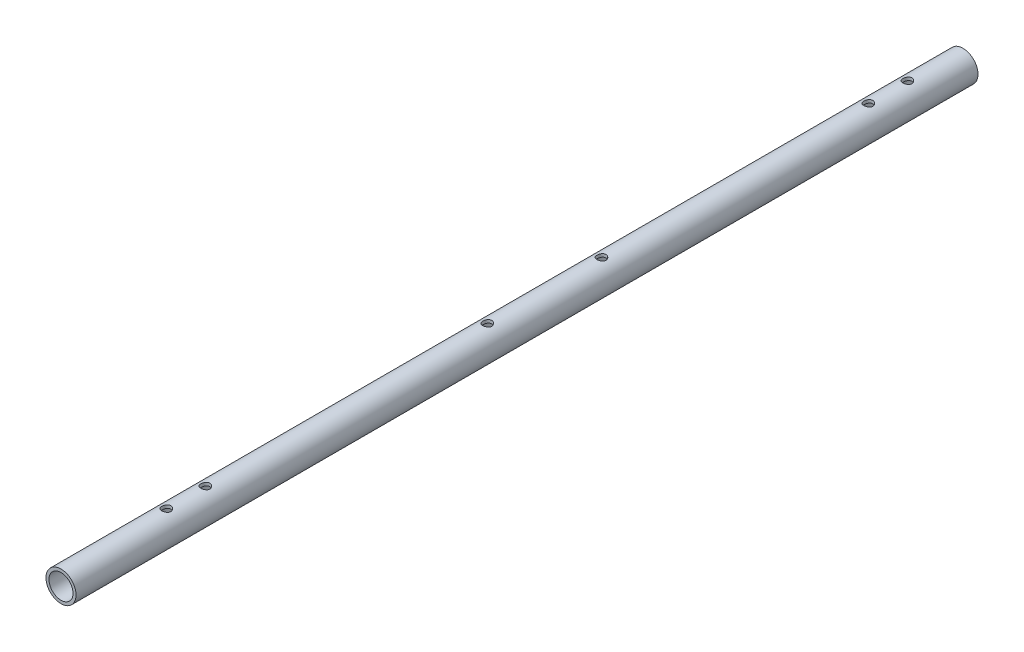
SolidWorks part; units mm, degrees
ref_plane "前视基准面" through (0, 0, 0) normal (0, 0, 1) x (1, 0, 0)
ref_plane "上视基准面" through (0, 0, 0) normal (0, 1, 0) x (1, 0, 0)
ref_plane "右视基准面" through (0, 0, 0) normal (1, 0, 0) x (0, 0, -1)
sketch "草图1" plane through (0, 0, 0) normal (0, 0, 1) x (1, 0, 0)
  circle A0 centre (0, 0) radius 5
  dimension "D1" = 10
extrude "拉伸-薄壁1" add sketch "草图1" along normal mid plane 300 thin thin type one direction reverse wall 1
sketch "草图2" plane through (0, 0, 0) normal (0, 1, 0) x (1, 0, 0)
  line L0 (0, 29.75) -> (0, -8.25) construction
  line L1 (-5, -150) -> (5, -150) construction
  circle A0 centre (0, 29.75) radius 1.5
  circle A1 centre (0, -8.25) radius 1.5
  circle A2 centre (0, 10.75) radius 1.5 construction
  dimension "D1" = 3
  dimension "D2" = 141.75
  dimension "D3" = 38
extrude "切除-拉伸1" cut sketch "草图2" against normal through all both and the other way through all
sketch "草图3" plane through (0, 0, 0) normal (0, 1, 0) x (0, 0, -1)
  line L0 (150, -5) -> (150, 5) construction
  line L1 (131.5, 0) -> (150, 0) construction
  line L2 (-115, 0) -> (-102, 0) construction
  line L3 (-150, 5) -> (-150, -5) construction
  circle A0 centre (118.5, 0) radius 1.5
  circle A1 centre (131.5, 0) radius 1.5
  circle A2 centre (-115, 0) radius 1.5
  circle A3 centre (-102, 0) radius 1.5
  point P11 (-108.5, 0)
  dimension "D1" = 13
  dimension "D2" = 3
  dimension "D3" = 18.5
  dimension "D4" = 13
  dimension "D5" = 41.5
extrude "切除-拉伸2" cut sketch "草图3" against normal through all both and the other way through all
